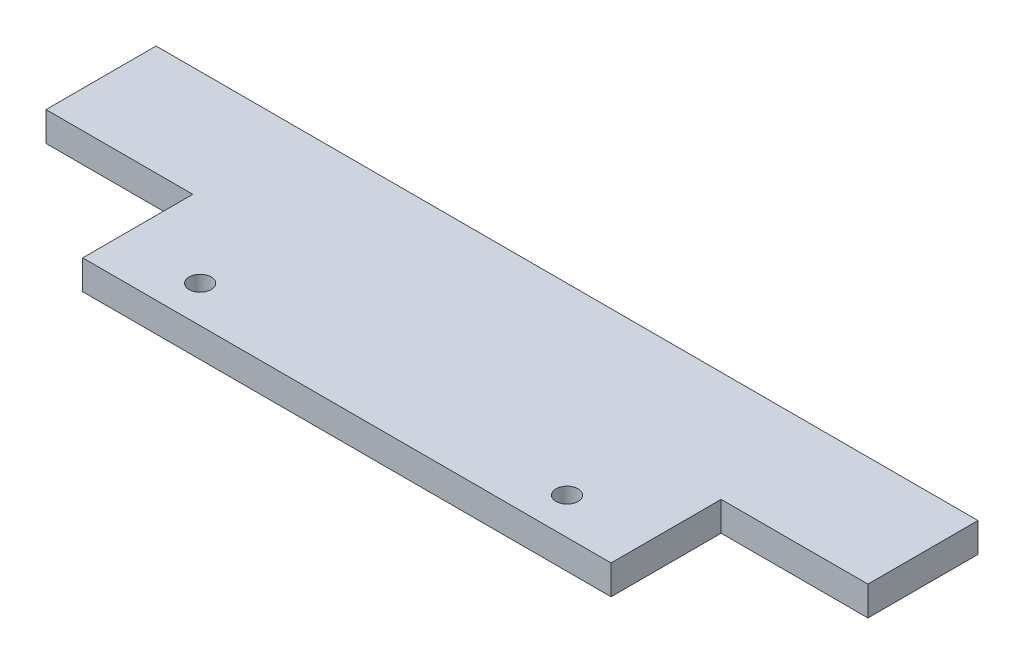
SolidWorks part; units mm, degrees
ref_plane "Front Plane" through (0, 0, 0) normal (0, 0, 1) x (1, 0, 0)
ref_plane "Top Plane" through (0, 0, 0) normal (0, 1, 0) x (1, 0, 0)
ref_plane "Right Plane" through (0, 0, 0) normal (1, 0, 0) x (0, 0, -1)
sketch "Sketch1" plane through (0, 0, 0) normal (0, 1, 0) x (1, 0, 0)
  line L1 (-32.1788, 13.6592) -> (39.8212, 13.6592)
  line L2 (-32.1788, 13.6592) -> (-32.1788, -16.3408)
  line L3 (-32.1788, -16.3408) -> (39.8212, -16.3408)
  line L4 (39.8212, 13.6592) -> (39.8212, -16.3408)
  dimension "D1" = 30
  dimension "D2" = 72
extrude "Boss-Extrude1" add sketch "Sketch1" along normal blind 4
sketch "Sketch2" plane through (0, 4, 0) normal (0, 1, 0) x (1, 0, 0)
  line L0 (-32.1788, 13.6592) -> (-32.1788, -16.3408) construction
  line L1 (-32.1788, -16.3408) -> (39.8212, -16.3408) construction
  line L2 (39.8212, -16.3408) -> (39.8212, 13.6592) construction
  circle A0 centre (-21.1788, -11.3408) radius 1.5
  circle A1 centre (28.8212, -11.3408) radius 1.5
  dimension "D1" = 3
  dimension "D2" = 11
  dimension "D3" = 5
  dimension "D4" = 3
  dimension "D5" = 11
  dimension "D6" = 5
extrude "Cut-Extrude1" cut sketch "Sketch2" against normal blind 4
sketch "Sketch3" plane through (0, 4, 0) normal (0, 1, 0) x (1, 0, 0)
  line L1 (39.8212, 13.6592) -> (59.8212, 13.6592)
  line L2 (39.8212, 13.6592) -> (39.8212, -1.3408)
  line L3 (39.8212, -1.3408) -> (59.8212, -1.3408)
  line L4 (59.8212, 13.6592) -> (59.8212, -1.3408)
  line L5 (-32.1788, 13.6592) -> (-52.1788, 13.6592)
  line L6 (-32.1788, 13.6592) -> (-32.1788, -1.3408)
  line L7 (-32.1788, -1.3408) -> (-52.1788, -1.3408)
  line L8 (-52.1788, 13.6592) -> (-52.1788, -1.3408)
  dimension "D1" = 15
  dimension "D2" = 20
  dimension "D3" = 20
  dimension "D4" = 15
extrude "Boss-Extrude3" add sketch "Sketch3" against normal blind 4
